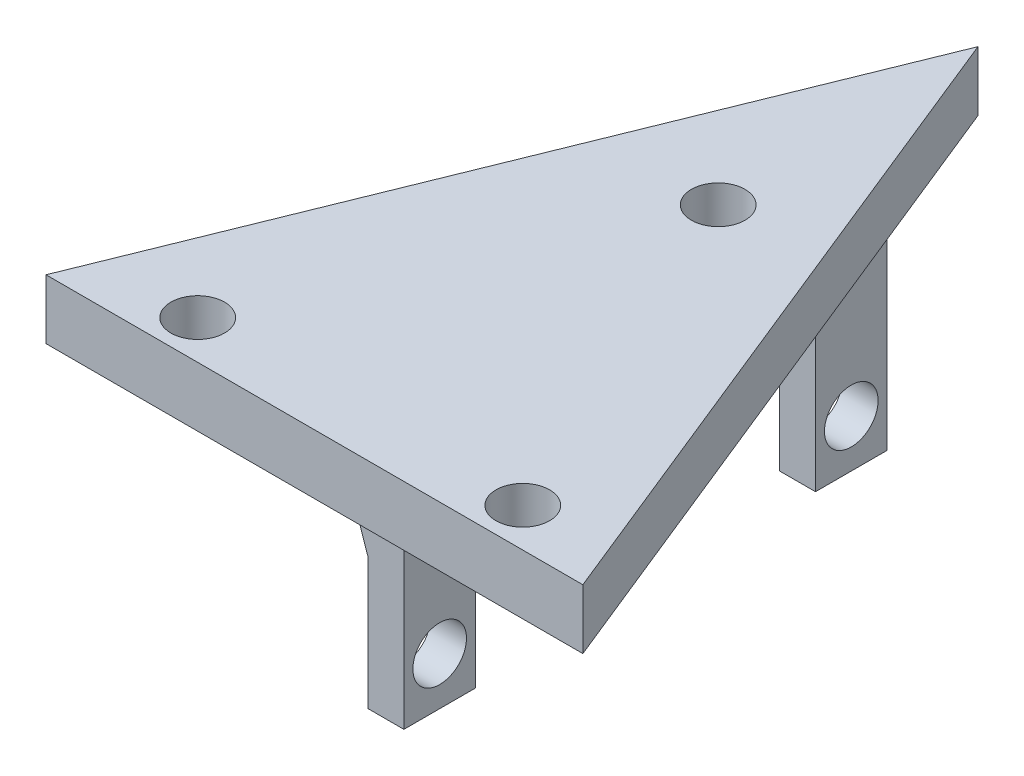
SolidWorks part; units mm, degrees
ref_plane "Front Plane" through (0, 0, 0) normal (0, 0, 1) x (1, 0, 0)
ref_plane "Top Plane" through (0, 0, 0) normal (0, 1, 0) x (1, 0, 0)
ref_plane "Right Plane" through (0, 0, 0) normal (1, 0, 0) x (0, 0, -1)
sketch "Sketch1" plane through (0, 0, 0) normal (0, 1, 0) x (1, 0, 0)
  line L0 (-14.339, 0) -> (30.661, 0)
  line L1 (30.661, 0) -> (8.161, 55.6215)
  line L2 (8.161, 55.6215) -> (-14.339, 0)
  dimension "D1" = 45
  dimension "D2" = 60
  dimension "D3" = 60
extrude "Boss-Extrude1" add sketch "Sketch1" along normal blind 5
hole_wizard "#8 Clearance Hole1" positions "3DSketch1" profile "Sketch2" hole size "#8" standard "ANSI Inch"
sketch3d "3DSketch1"
  line L0 (-14.339, 0, 0) -> (30.661, 0, 0) construction
  line L1 (30.661, 0, 0) -> (8.161, 0, -55.6215) construction
  line L2 (8.161, 0, -55.6215) -> (-14.339, 0, 0) construction
  point P0 (22.3778, 0, -3.25)
  point P2 (-4.8722, 0, -3.25)
  point P4 (8.7528, 0, -33.251)
  dimension "D1" = 27.25
  dimension "D2" = 3.25
  dimension "D3" = 3.25
  dimension "D4" = 6.46
  dimension "D5" = 7.5572
  dimension "D6" = 32.95
  dimension "D7" = 32.95
sketch "Sketch2" plane through (22.3778, 0, -3.25) normal (1, 0, 0) x (0, 0, -1)
  line L0 (0, 0) -> (0, 18.3507)
  line L1 (0, 18.3507) -> (2.2479, 17)
  line L2 (2.2479, 17) -> (2.2479, 0)
  line L5 (2.2479, 0) -> (0, 0)
  line L10 (0, 18.3507) -> (-2.2479, 17) construction
  line L11 (0, -6.35) -> (0, 107.95) construction
  dimension "Hole Dia." = 4.4958
  dimension "Hole Depth" = 17
  dimension "Drill Angle" = 118
sketch "Sketch3" plane through (0, 0, 0) normal (0, -1, 0) x (-1, 0, 0)
  line L1 (-7.661, 45.5) -> (-10.661, 45.5)
  line L2 (-7.661, 45.5) -> (-7.661, 39.5)
  line L3 (-7.661, 39.5) -> (-10.661, 39.5)
  line L4 (-10.661, 45.5) -> (-10.661, 39.5)
  line L5 (-7.661, 11) -> (-10.661, 11)
  line L6 (-7.661, 11) -> (-7.661, 5)
  line L7 (-7.661, 5) -> (-10.661, 5)
  line L8 (-10.661, 11) -> (-10.661, 5)
  line L10 (14.339, 0) -> (-30.661, 0) construction
  dimension "D1" = 34.5
  dimension "D2" = 6
  dimension "D3" = 6
  dimension "D4" = 3
  dimension "D5" = 3
  dimension "D8" = 5
extrude "Boss-Extrude2" add sketch "Sketch3" along normal blind 18
sketch "Sketch17" plane through (0, 0, -45.5) normal (0, 0, -1) x (-1, 0, 0)
  line L0 (-7.661, -7) -> (-5.161, 0)
  line L1 (-7.661, -18) -> (-7.661, 0) construction
  dimension "D1" = 2.5
  dimension "D2" = 11
rib "Rib2" sketch "Sketch17" sketch "Sketch17" thickness 6 extrusion direction parallel to sketch draft on no parameters "D1"=6
sketch "Sketch18" plane through (0, 0, -11) normal (0, 0, -1) x (-1, 0, 0)
  line L0 (-7.661, -7) -> (-5.161, 0.2729)
  line L1 (-7.661, -18) -> (-7.661, 0) construction
  dimension "D1" = 11
  dimension "D2" = 2.5
rib "Rib3" sketch "Sketch18" sketch "Sketch18" thickness 6 extrusion direction parallel to sketch draft on no parameters "D1"=6
hole_wizard "#8 Clearance Hole2" positions "3DSketch2" profile "Sketch16" hole size "#8" standard "ANSI Inch"
sketch3d "3DSketch2"
  line L0 (7.661, -18, -45.5) -> (7.661, -7, -45.5) construction
  line L1 (7.661, -18, -11) -> (7.661, -7, -11) construction
  line L2 (7.661, -18, -39.5) -> (7.661, -18, -45.5) construction
  line L3 (7.661, -18, -5) -> (7.661, -18, -11) construction
  point P0 (7.661, -14, -42.5)
  point P2 (7.661, -14, -8)
  dimension "D1" = 3
  dimension "D2" = 3
  dimension "D3" = 4
  dimension "D4" = 4
sketch "Sketch16" plane through (7.661, -14, -42.5) normal (0, 1, 0) x (0, 0, 1)
  line L0 (0, 0) -> (0, 18.3507)
  line L1 (0, 18.3507) -> (2.2479, 17)
  line L2 (2.2479, 17) -> (2.2479, 0)
  line L5 (2.2479, 0) -> (0, 0)
  line L10 (0, 18.3507) -> (-2.2479, 17) construction
  line L11 (0, -6.35) -> (0, 107.95) construction
  dimension "Hole Dia." = 4.4958
  dimension "Hole Depth" = 17
  dimension "Drill Angle" = 118
